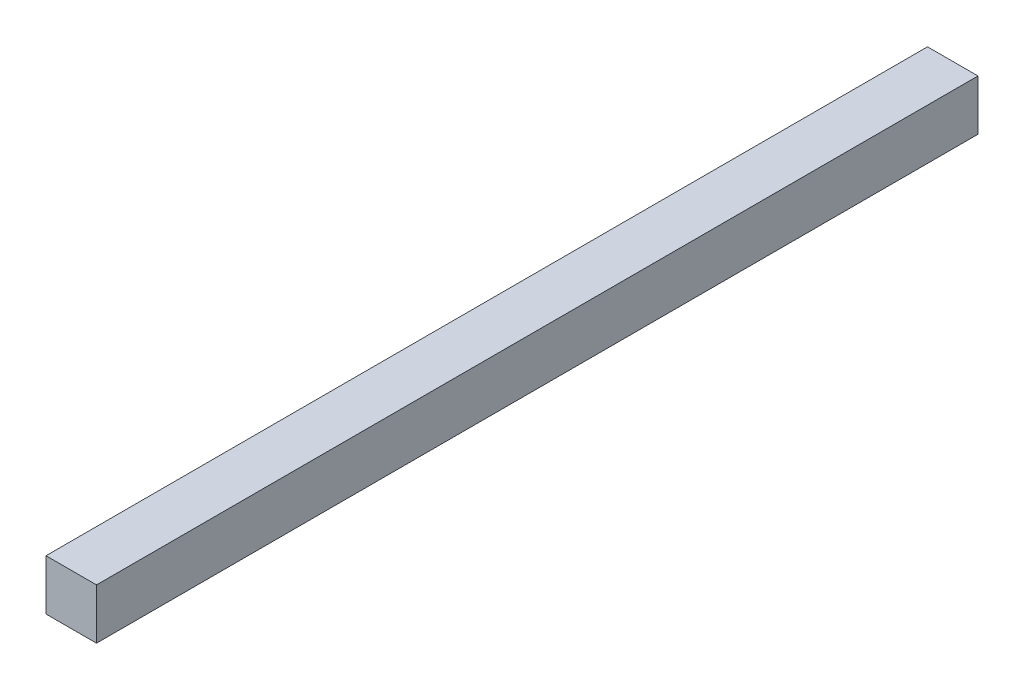
SolidWorks part; units mm, degrees
ref_plane "Front Plane" through (0, 0, 0) normal (0, 0, 1) x (1, 0, 0)
ref_plane "Top Plane" through (0, 0, 0) normal (0, 1, 0) x (1, 0, 0)
ref_plane "Right Plane" through (0, 0, 0) normal (1, 0, 0) x (0, 0, -1)
sketch "Sketch1" plane through (0, 0, 0) normal (0, 0, 1) x (1, 0, 0)
  line L0 (0, 17.4625) -> (0, -17.4625)
  line L1 (-17.4625, 0) -> (17.4625, 0) construction
  point P6 (0, 0)
  dimension "Width" = 34.925
  dimension "Thk" = 34.925
sketch "Sketch2" plane through (0, 0, 0) normal (1, 0, 0) x (0, 0, -1)
  line L0 (457.2, 0) -> (-457.2, 0)
  point P4 (0, 0)
  dimension "Length" = 914.4
sketch "Sketch3" plane through (0, 0, 0) normal (0, 0, 1) x (1, 0, 0)
  line L1 (17.4625, 17.4625) -> (-17.4625, 17.4625)
  line L2 (17.4625, 17.4625) -> (17.4625, -17.4625)
  line L3 (17.4625, -17.4625) -> (-17.4625, -17.4625)
  line L4 (-17.4625, 17.4625) -> (-17.4625, -17.4625)
  line L5 (17.4625, 17.4625) -> (-17.4625, -17.4625) construction
  line L6 (17.4625, -17.4625) -> (-17.4625, 17.4625) construction
  point P0 (0, 0)
extrude "Boss-Extrude1" add sketch "Sketch3" along normal blind 609.6
